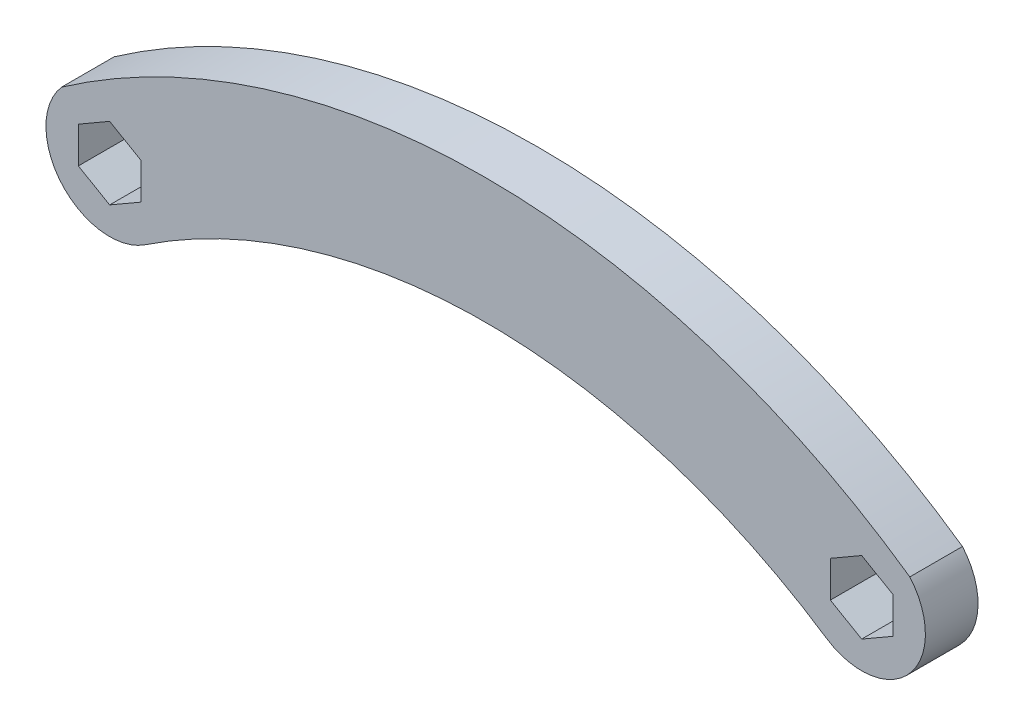
SolidWorks part; units mm, degrees
ref_plane "Front Plane" through (0, 0, 0) normal (0, 0, 1) x (1, 0, 0)
ref_plane "Top Plane" through (0, 0, 0) normal (0, 1, 0) x (1, 0, 0)
ref_plane "Right Plane" through (0, 0, 0) normal (1, 0, 0) x (0, 0, -1)
sketch "Sketch1" plane through (0, 0, 0) normal (0, 0, 1) x (1, 0, 0)
  line L1 (0, 93.4443) -> (0, -85.4532) construction
  line L2 (-38.1, 60.8162) -> (-41.275, 58.9831)
  line L3 (-41.275, 58.9831) -> (-41.275, 55.3169)
  line L4 (-41.275, 55.3169) -> (-38.1, 53.4838)
  line L5 (-38.1, 53.4838) -> (-34.925, 55.3169)
  line L6 (-34.925, 55.3169) -> (-34.925, 58.9831)
  line L7 (-34.925, 58.9831) -> (-38.1, 60.8162)
  line L8 (38.1, 60.8162) -> (34.925, 58.9831)
  line L9 (34.925, 58.9831) -> (34.925, 55.3169)
  line L10 (34.925, 55.3169) -> (38.1, 53.4838)
  line L11 (38.1, 53.4838) -> (41.275, 55.3169)
  line L12 (41.275, 55.3169) -> (41.275, 58.9831)
  line L13 (41.275, 58.9831) -> (38.1, 60.8162)
  arc A0 (42.9771, 61.3798) -> (-42.9771, 61.3798) centre (0, 0) ccw
  circle A1 centre (-38.1, 57.15) radius 1.5 construction
  circle A2 centre (38.1, 57.15) radius 1.5 construction
  arc A3 (34.519, 51.7785) -> (-34.519, 51.7785) centre (0, 0) ccw
  arc A4 (-42.9771, 61.3798) -> (-34.519, 51.7785) centre (-38.1, 57.15) ccw
  arc A5 (42.9771, 61.3798) -> (34.519, 51.7785) centre (38.1, 57.15) cw
  circle A6 centre (-38.1, 57.15) radius 3.175 construction
  circle A7 centre (38.1, 57.15) radius 3.175 construction
  dimension "D1" = 149.86
  dimension "D3" = 3
  dimension "D4" = 38.1
  dimension "D6" = 124.46
  dimension "D2" = 6.35
  dimension "D5" = 57.15
extrude "Boss-Extrude1" add sketch "Sketch1" along normal blind 5.334
sketch "Sketch3" plane through (0, 0, 5.334) normal (0, 0, 1) x (1, 0, 0)
  line L0 (0, 98.585) -> (0, -80.3125) construction
  line L1 (-38.1, 60.8162) -> (-41.275, 58.9831)
  line L2 (-41.275, 58.9831) -> (-41.275, 55.3169)
  line L3 (-41.275, 55.3169) -> (-38.1, 53.4838)
  line L4 (-38.1, 53.4838) -> (-34.925, 55.3169)
  line L5 (-34.925, 55.3169) -> (-34.925, 58.9831)
  line L6 (-34.925, 58.9831) -> (-38.1, 60.8162)
  line L7 (38.1, 60.8162) -> (34.925, 58.9831)
  line L8 (34.925, 58.9831) -> (34.925, 55.3169)
  line L9 (34.925, 55.3169) -> (38.1, 53.4838)
  line L10 (38.1, 53.4838) -> (41.275, 55.3169)
  line L11 (41.275, 55.3169) -> (41.275, 58.9831)
  line L12 (41.275, 58.9831) -> (38.1, 60.8162)
  arc A0 (42.9771, 61.3798) -> (-42.9771, 61.3798) centre (0, 0) ccw
  circle A1 centre (-38.1, 57.15) radius 1.5 construction
  circle A2 centre (38.1, 57.15) radius 1.5 construction
  arc A3 (34.519, 51.7785) -> (-34.519, 51.7785) centre (0, 0) ccw
  arc A4 (-42.9771, 61.3798) -> (-34.519, 51.7785) centre (-38.1, 57.15) ccw
  arc A5 (42.9771, 61.3798) -> (34.519, 51.7785) centre (38.1, 57.15) cw
  circle A6 centre (-38.1, 57.15) radius 3.175 construction
  circle A7 centre (38.1, 57.15) radius 3.175 construction
  arc A8 (34.519, 51.7785) -> (-34.519, 51.7785) centre (0, 0) ccw construction
  point P25 (0, 62.23)
  point P29 (0, 62.23)
  dimension "D1" = 149.86
  dimension "D2" = 3
  dimension "D5" = 124.46
  dimension "D6" = 6.35
  dimension "D3" = 38.1
  dimension "D4" = 57.15
